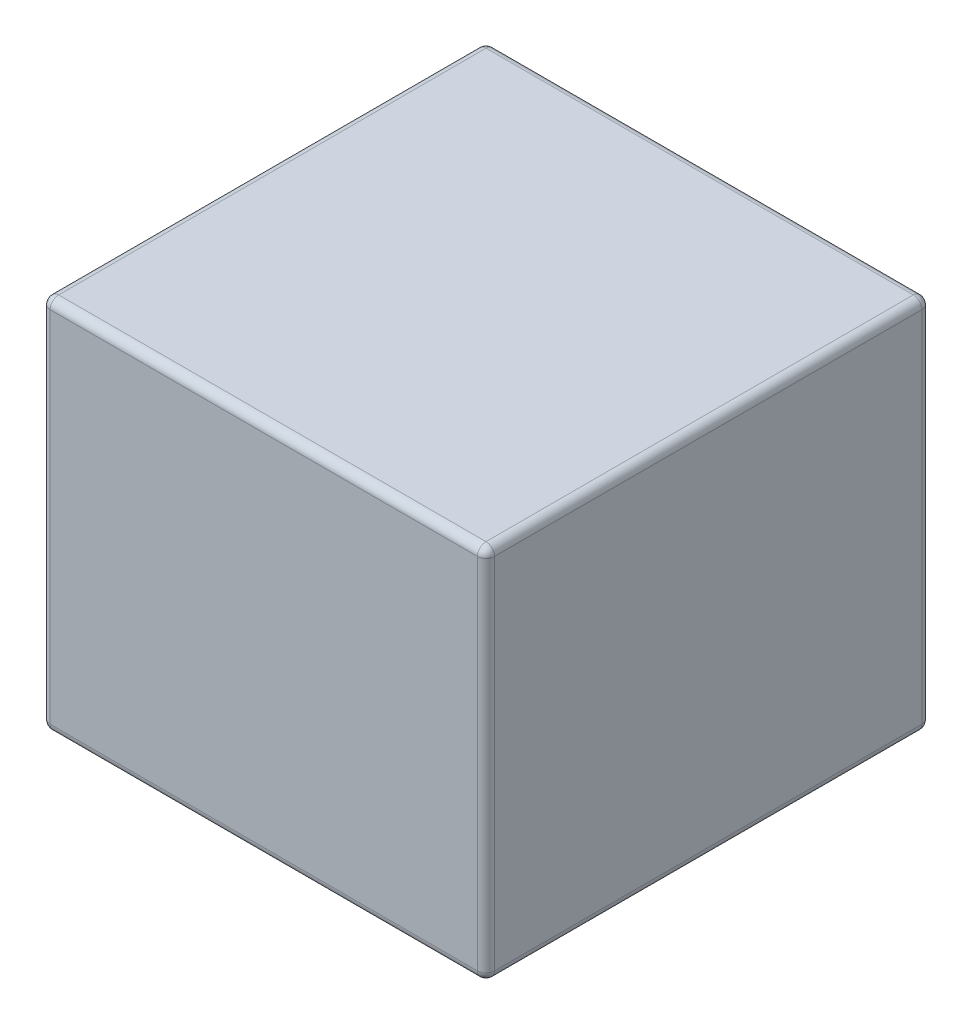
SolidWorks part; units mm, degrees
ref_plane "Front Plane" through (0, 0, 0) normal (0, 0, 1) x (1, 0, 0)
ref_plane "Top Plane" through (0, 0, 0) normal (0, 1, 0) x (1, 0, 0)
ref_plane "Right Plane" through (0, 0, 0) normal (1, 0, 0) x (0, 0, -1)
sketch "Sketch1" plane through (0, 0, 0) normal (0, 1, 0) x (1, 0, 0)
  line L1 (0, 0) -> (330.2, 0)
  line L2 (0, 0) -> (0, 330.2)
  line L3 (0, 330.2) -> (330.2, 330.2)
  line L4 (330.2, 0) -> (330.2, 330.2)
  dimension "D1" = 330.2
  dimension "D2" = 330.2
extrude "Boss-Extrude1" add sketch "Sketch1" along normal blind 279.4
fillet "Fillet1" radius 6.35 12 edges at (0, 0, -165.1) (0, 139.7, -330.2) (165.1, 0, -330.2) (330.2, 139.7, -330.2) (330.2, 0, -165.1) (0, 139.7, 0) (330.2, 139.7, 0) (165.1, 0, 0) (165.1, 279.4, -330.2) (330.2, 279.4, -165.1) (165.1, 279.4, 0) (0, 279.4, -165.1)
ref_plane "Mid_Plane" through (165.1, 0, 0) normal (1, 0, 0) x (0, 0, -1)
ref_plane "Plane1" through (0, 139.7, 0) normal (0, 1, 0) x (1, 0, 0)
